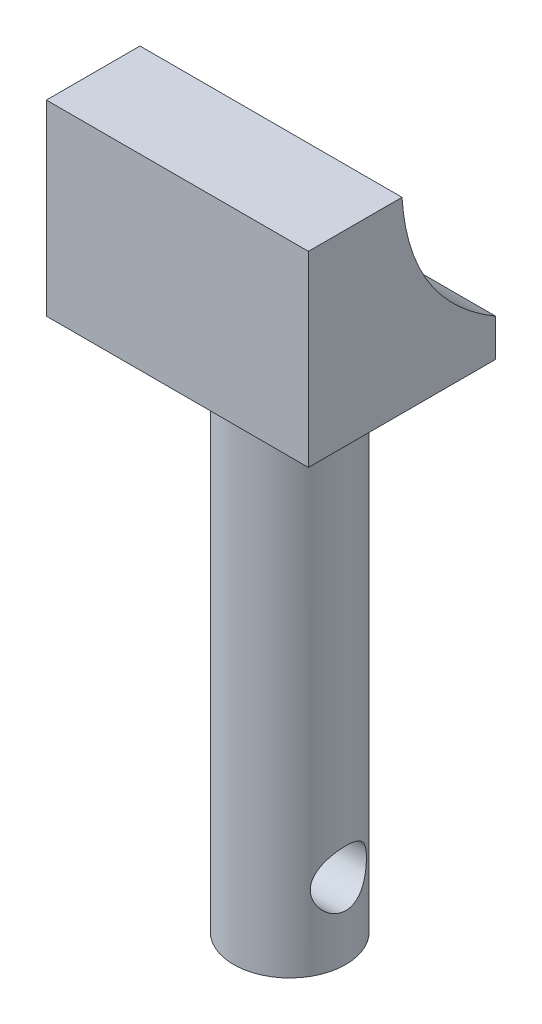
SolidWorks part; units mm, degrees
ref_plane "Front Plane" through (0, 0, 0) normal (0, 0, 1) x (1, 0, 0)
ref_plane "Top Plane" through (0, 0, 0) normal (0, 1, 0) x (1, 0, 0)
ref_plane "Right Plane" through (0, 0, 0) normal (1, 0, 0) x (0, 0, -1)
sketch "Sketch1" plane through (0, 0, 0) normal (0, 0, 1) x (1, 0, 0)
  line L1 (-4.6999, 4.6725) -> (2.3001, 4.6725)
  line L2 (-4.6999, 4.6725) -> (-4.6999, -0.3275)
  line L3 (-4.6999, -0.3275) -> (2.3001, -0.3275)
  line L4 (2.3001, 4.6725) -> (2.3001, -0.3275)
  dimension "D1" = 7
  dimension "D2" = 5
extrude "Boss-Extrude1" add sketch "Sketch1" along normal blind 5
sketch "Sketch2" plane through (-4.6999, 0, 0) normal (-1, 0, 0) x (0, 0, 1)
  line L0 (0, 0.6725) -> (5, 0.6725) construction
  line L3 (5, 4.6725) -> (0, 4.6725) construction
  line L4 (2.5, 4.6725) -> (0, 4.6725)
  line L5 (0, 4.6725) -> (0, 0.6725)
  line L7 (5, -0.3275) -> (0, -0.3275) construction
  spline S0 degree 2 poles (0, 0.6725) (2.331, 2.0397) (2.5, 4.6725) knots 0 0 0 1 1 1
  dimension "D1" = 1
extrude "Cut-Extrude1" cut sketch "Sketch2" against normal blind 7
sketch "Sketch3" plane through (0, 0, 0) normal (0, 0, -1) x (-1, 0, 0)
  line L0 (-2.3001, -0.3275) -> (-2.3001, 0.6725) construction
  line L1 (-2.3001, 1.1725) -> (4.6999, 1.1725)
  line L2 (-2.3001, 1.1725) -> (-2.3001, -0.3275)
  line L3 (-2.3001, -0.3275) -> (4.6999, -0.3275)
  line L4 (4.6999, 1.1725) -> (4.6999, -0.3275)
  dimension "D1" = 1.5
extrude "Boss-Extrude2" [suppressed] add sketch "Sketch3" along normal up to surface (5.85 mm away)
sketch "Sketch4" plane through (0, -0.3275, 0) normal (0, -1, 0) x (1, 0, 0)
  line L0 (-4.6999, 2.5) -> (2.3001, 2.5) construction
  line L1 (2.3001, 5) -> (2.3001, 0) construction
  line L2 (-4.6999, 0) -> (2.3001, 0) construction
  circle A1 centre (-1.1999, 2) radius 1.5
  point P12 (-1.1999, 2.5)
  dimension "D1" = 3
  dimension "D2" = 2
extrude "Boss-Extrude3" add sketch "Sketch4" along normal blind 14
ref_plane "Plane1" through (0, 0, 5) normal (0, 0, 1) x (1, 0, 0)
hole_wizard "Ø1.5mm Dowel Hole1" [suppressed] positions "Sketch6" profile "Sketch7" hole size "Ø1.5" standard "ISO"
sketch "Sketch6" plane through (0, 0, 5) normal (0, 0, 1) x (1, 0, 0)
  line L0 (-2.6999, -14.3275) -> (0.3001, -14.3275)
  line L2 (-1.1999, -14.3275) -> (-1.1999, -10.2365)
  point P0 (-1.1999, -12.8275)
  dimension "D1" = 1.5
sketch "Sketch7" plane through (-1.1999, -12.8275, 5) normal (1, 0, 0) x (0, -1, 0)
  line L0 (0, 0) -> (0, 5)
  line L1 (0, 5) -> (0.75, 5)
  line L2 (0.75, 5) -> (0.75, 0)
  line L5 (0.75, 0) -> (0, 0)
  line L11 (0, -6.35) -> (0, 107.95) construction
  dimension "Thru Hole Dia." = 1.5
  dimension "Thru Hole Depth" = 5
ref_plane "Plane2" through (-4.6999, 0, 0) normal (-1, 0, 0) x (0, 0, 1)
hole_wizard "Ø1.5mm Dowel Hole2" positions "Sketch9" profile "Sketch8" hole size "Ø1.5" standard "ISO" end condition through all
sketch "Sketch9" plane through (-4.6999, 0, 0) normal (-1, 0, 0) x (0, 0, 1)
  line L0 (0.5, -14.3275) -> (3.5, -14.3275) construction
  line L1 (3.5, -14.3275) -> (3.5, -0.3275) construction
  point P0 (2, -12.3275)
  dimension "D1" = 2
  dimension "D2" = 1.5
sketch "Sketch8" plane through (-4.6999, -12.3275, 2) normal (0, 1, 0) x (0, 0, 1)
  line L0 (0, 0) -> (0, 7)
  line L1 (0, 7) -> (0.75, 7)
  line L2 (0.75, 7) -> (0.75, 0)
  line L5 (0.75, 0) -> (0, 0)
  line L11 (0, -6.35) -> (0, 107.95) construction
  dimension "Thru Hole Dia." = 1.5
  dimension "Thru Hole Depth" = 7
